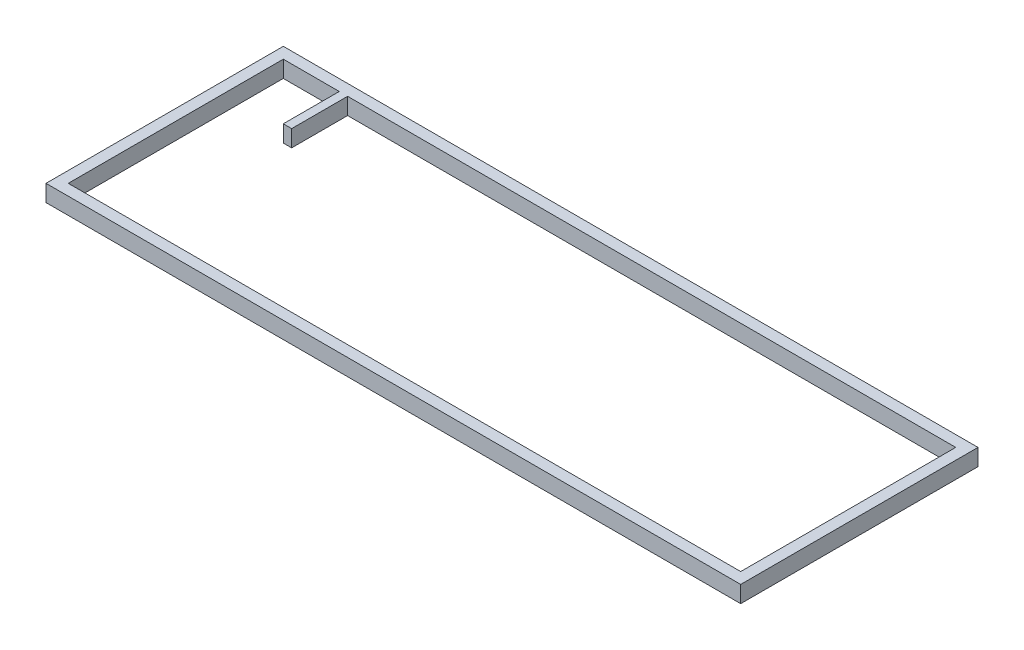
SolidWorks part; units mm, degrees
ref_plane "Plan de face" through (0, 0, 0) normal (0, 0, 1) x (1, 0, 0)
ref_plane "Plan de dessus" through (0, 0, 0) normal (0, 1, 0) x (1, 0, 0)
ref_plane "Plan de droite" through (0, 0, 0) normal (1, 0, 0) x (0, 0, -1)
sketch "Esquisse1" plane through (0, 0, 0) normal (0, 1, 0) x (1, 0, 0)
  line L0 (27.1, 81.25) -> (245.56, 81.25)
  line L1 (0, 0) -> (249.56, 0)
  line L2 (0, 0) -> (0, 85.25)
  line L3 (0, 85.25) -> (249.56, 85.25)
  line L4 (249.56, 0) -> (249.56, 85.25)
  line L5 (4, 81.25) -> (24.1, 81.25)
  line L6 (4, 81.25) -> (4, 4)
  line L7 (4, 4) -> (245.56, 4)
  line L8 (245.56, 81.25) -> (245.56, 4)
  line L10 (24.1, 81.25) -> (24.1, 61.15)
  line L11 (24.1, 61.15) -> (27.1, 61.15)
  line L12 (27.1, 81.25) -> (27.1, 61.15)
  dimension "D1" = 249.56
  dimension "D2" = 85.25
  dimension "D3" = 4
  dimension "D4" = 4
  dimension "D5" = 4
  dimension "D6" = 4
  dimension "D7" = 20.1
  dimension "D8" = 20.1
  dimension "D9" = 3
extrude "Boss.-Extru.1" add sketch "Esquisse1" along normal blind 6
equation "\"L_ext\"=300"
equation "\"H_sw_plate\"=100"
equation "\"L_sw_plate\"=250"
